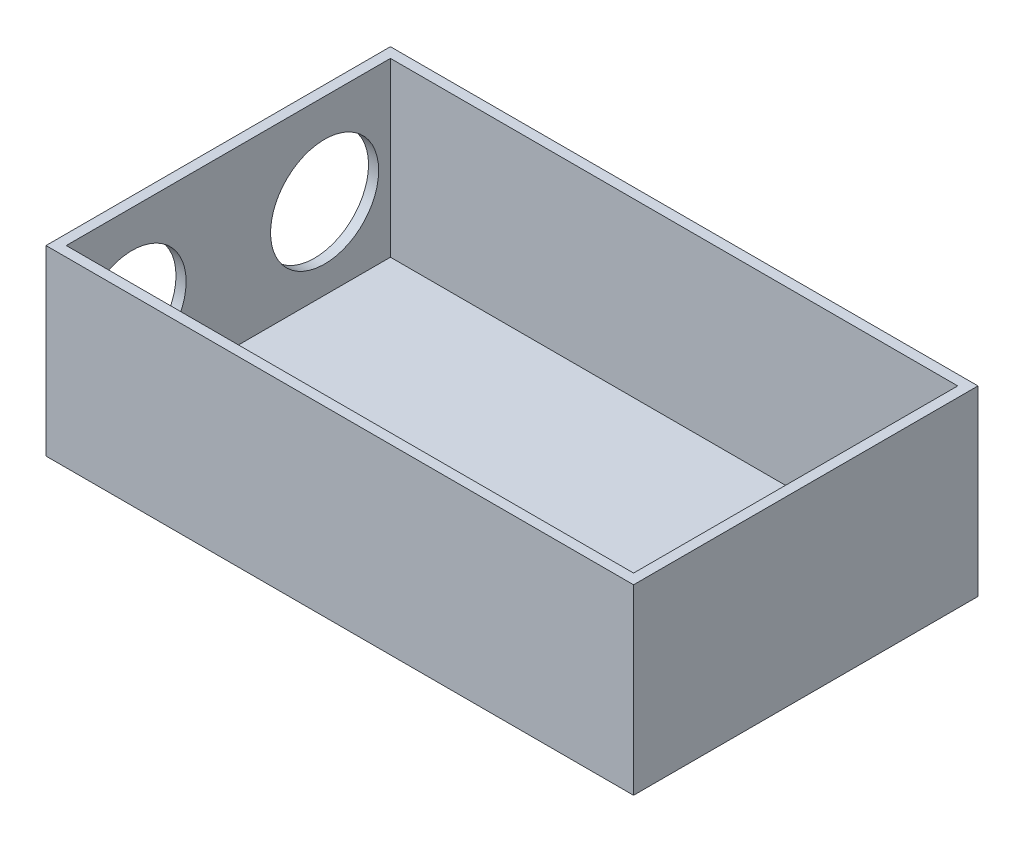
SolidWorks part; units mm, degrees
ref_plane "Front Plane" through (0, 0, 0) normal (0, 0, 1) x (1, 0, 0)
ref_plane "Top Plane" through (0, 0, 0) normal (0, 1, 0) x (1, 0, 0)
ref_plane "Right Plane" through (0, 0, 0) normal (1, 0, 0) x (0, 0, -1)
sketch "Sketch1" plane through (0, 0, 0) normal (0, 1, 0) x (1, 0, 0)
  line L0 (-200, 105) -> (180, 105) construction
  line L1 (-300, -125) -> (300, -125) construction
  line L2 (-300, -125) -> (-300, 125) construction
  line L3 (-300, 125) -> (300, 125) construction
  line L4 (300, -125) -> (300, 125) construction
  line L5 (-200, 47.5) -> (41.3, 47.5) construction
  line L6 (-200, -47.5) -> (41.3, -47.5) construction
  line L7 (-200, 125) -> (180, 125) construction
  line L8 (-200, 125) -> (-200, -125) construction
  line L9 (-200, -125) -> (180, -125) construction
  line L10 (180, 125) -> (180, -125) construction
  line L11 (-200, -85) -> (180, -85) construction
  line L12 (-200, -85) -> (-200, 85) construction
  line L13 (-200, 85) -> (180, 85) construction
  line L14 (180, -85) -> (180, 85) construction
  line L15 (-438.021, 0) -> (438.021, 0) construction
  line L16 (-200, -105) -> (180, -105) construction
  line L18 (-435.6719, 0) -> (360.7299, 0) construction
  point P0 (0, 0)
  point P6 (0, 0)
  point P11 (0, 0)
  point P22 (0, 125)
  point P24 (300, 0)
  point P27 (-200, 0)
  dimension "D1" = 600
  dimension "D2" = 250
  dimension "D3" = 100
  dimension "D4" = 120
  dimension "D5" = 380
  dimension "D6" = 170
  dimension "D7" = 85
  dimension "D8" = 20
  dimension "D9" = 47.5
  dimension "D10" = 241.3
  dimension "D11" = 20
sketch "Sketch4" plane through (0, 0, 0) normal (0, 1, 0) x (1, 0, 0)
  line L0 (180, 85) -> (180, -85)
  line L1 (180, 85) -> (-110, 85)
  line L2 (180, -85) -> (-110, -85)
  line L3 (-110, 85) -> (-110, -85)
  line L4 (-435.6719, 0) -> (360.7299, 0) construction
  point P3 (180, 0)
  dimension "D1" = 290
  dimension "D2" = 170
extrude "Boss-Extrude1" add sketch "Sketch4" along normal mid plane 90
shell "Shell1" thickness 5
sketch "Sketch5" plane through (-110, 0, 0) normal (-1, 0, 0) x (0, 0, 1)
  line L0 (0, -55) -> (0, 55) construction
  circle A0 centre (-47.515, 0) radius 26.67
  circle A1 centre (47.515, 0) radius 26.67
extrude "Cut-Extrude1" cut sketch "Sketch5" against normal mid plane 80
